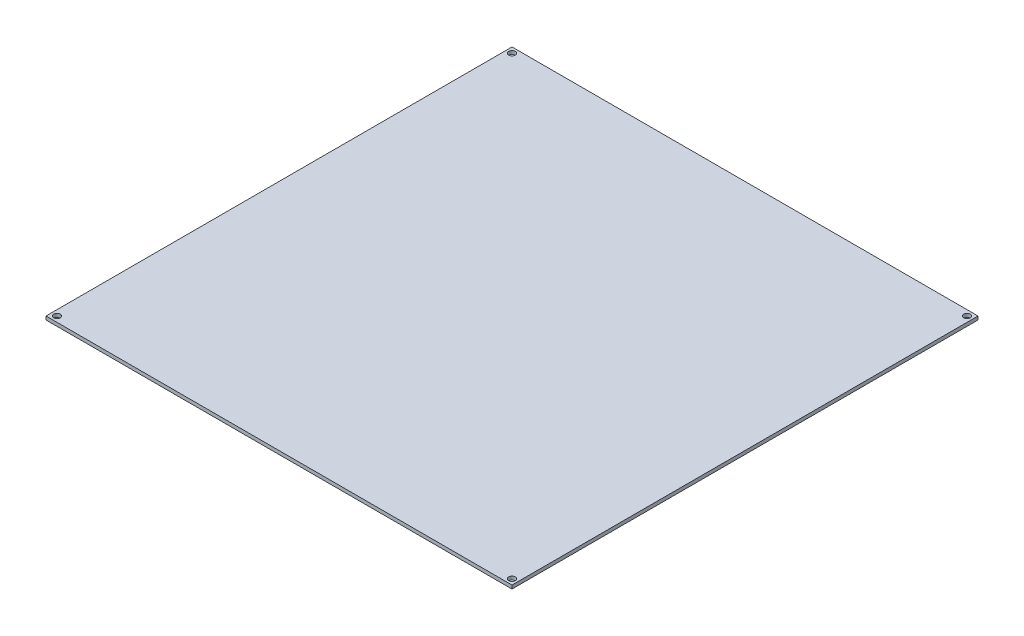
SolidWorks part; units mm, degrees
ref_plane "Front Plane" through (0, 0, 0) normal (0, 0, 1) x (1, 0, 0)
ref_plane "Top Plane" through (0, 0, 0) normal (0, 1, 0) x (1, 0, 0)
ref_plane "Right Plane" through (0, 0, 0) normal (1, 0, 0) x (0, 0, -1)
sketch "Sketch1" plane through (0, 0, 0) normal (0, 1, 0) x (1, 0, 0)
  line L1 (-107, -107) -> (107, -107)
  line L2 (-107, -107) -> (-107, 107)
  line L3 (-107, 107) -> (107, 107)
  line L4 (107, -107) -> (107, 107)
  line L5 (-107, -107) -> (107, 107) construction
  line L6 (-107, 107) -> (107, -107) construction
  circle A0 centre (-104.5, 104.5) radius 1.5
  circle A1 centre (104.5, 104.5) radius 1.5
  circle A2 centre (104.5, -104.5) radius 1.5
  circle A3 centre (-104.5, -104.5) radius 1.5
  point P0 (0, 0)
  dimension "D2" = 3
  dimension "D1" = 214
  dimension "D3" = 2.5
  dimension "D4" = 2.5
  dimension "D5" = 2.5
  dimension "D6" = 2.5
extrude "Boss-Extrude1" add sketch "Sketch1" along normal blind 1.6
